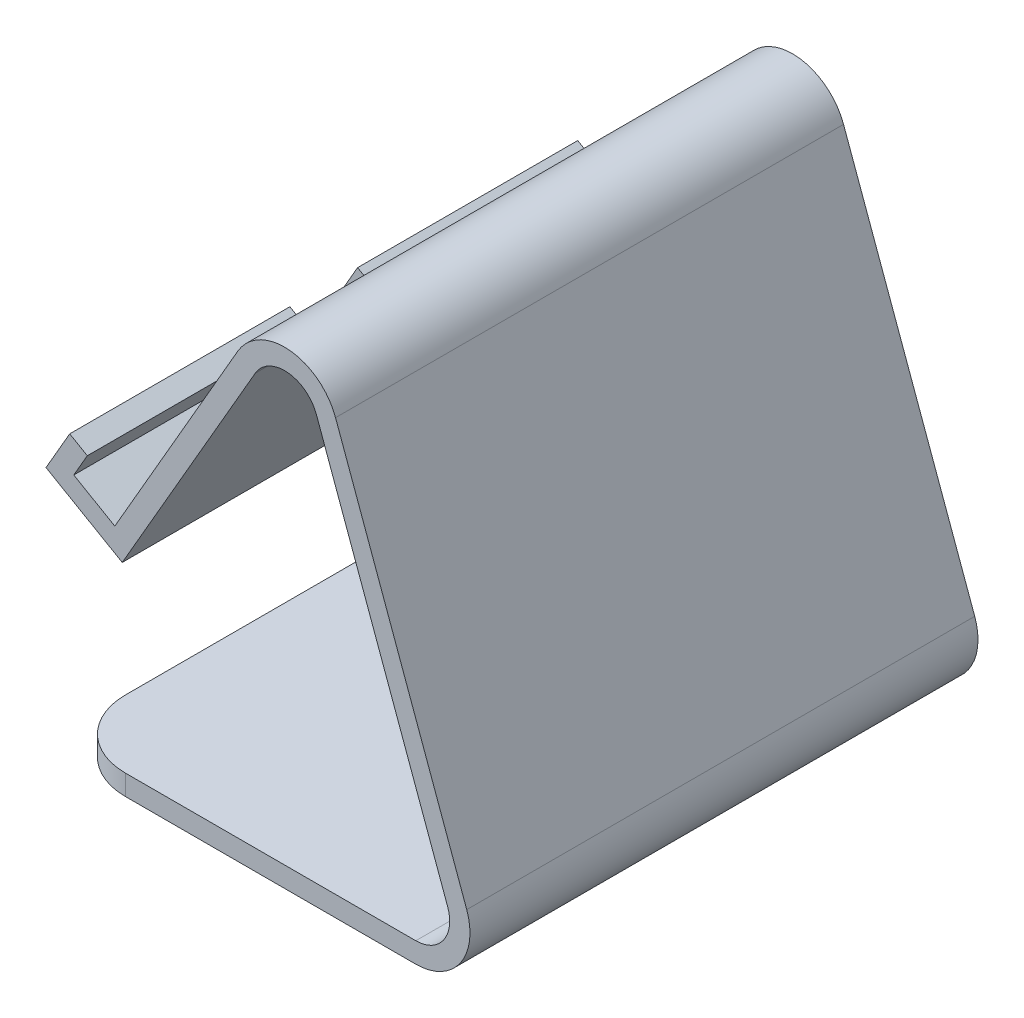
SolidWorks part; units mm, degrees
ref_plane "前视基准面" through (0, 0, 0) normal (0, 0, 1) x (1, 0, 0)
ref_plane "上视基准面" through (0, 0, 0) normal (0, 1, 0) x (1, 0, 0)
ref_plane "右视基准面" through (0, 0, 0) normal (1, 0, 0) x (0, 0, -1)
other "Configuration Table"
sketch "草图1" plane through (0, 0, 0) normal (0, 0, 1) x (1, 0, 0)
  line L0 (0, 0) -> (52.8593, 0)
  line L1 (57.5577, 6.7101) -> (38.1894, 59.9241)
  line L2 (29.1608, 60.714) -> (9.5221, 26.6987)
  line L3 (9.5221, 26.6987) -> (-1.7362, 33.1987)
  line L4 (-1.7362, 33.1987) -> (1.7638, 39.2609)
  line L5 (0, -3) -> (52.8593, -3)
  line L6 (60.3768, 7.7362) -> (41.0085, 60.9502)
  line L7 (26.5627, 62.214) -> (8.424, 30.7968)
  line L8 (8.424, 30.7968) -> (2.3618, 34.2968)
  line L9 (2.3618, 34.2968) -> (4.3618, 37.7609)
  line L10 (1.7638, 39.2609) -> (4.3618, 37.7609)
  line L11 (0, 0) -> (0, -3)
  arc A0 (38.1894, 59.9241) -> (29.1608, 60.714) centre (33.4909, 58.214) ccw
  arc A1 (52.8593, 0) -> (57.5577, 6.7101) centre (52.8593, 5) ccw
  arc A2 (52.8593, -3) -> (60.3768, 7.7362) centre (52.8593, 5) ccw
  arc A3 (41.0085, 60.9502) -> (26.5627, 62.214) centre (33.4909, 58.214) ccw
  point P9 (34.5221, 70)
  point P12 (60, 0)
  dimension "D8" = 5
  dimension "D9" = 5
  dimension "D1" = 60
  dimension "D2" = 70
  dimension "D3" = 70
  dimension "D4" = 50
  dimension "D5" = 13
  dimension "D6" = 7
  dimension "D7" = 50
  dimension "D10" = 3
extrude "凸台-拉伸2" add sketch "草图1" along normal mid plane 75
sketch "草图2" plane through (-15.6777, 9.0515, 0) normal (-0.866, 0.5, 0) x (0, 0, 1)
  line L0 (37.5, 27.8828) -> (-37.5, 27.8828) construction
  line L1 (-5, 35.3828) -> (5, 35.3828)
  line L2 (-5, 35.3828) -> (-5, 20.3828)
  line L3 (-5, 20.3828) -> (5, 20.3828)
  line L4 (5, 35.3828) -> (5, 20.3828)
  line L5 (-5, 35.3828) -> (5, 20.3828) construction
  line L6 (-5, 20.3828) -> (5, 35.3828) construction
  point P0 (0, 27.8828)
  point P9 (0, 0)
  dimension "D1" = 15
  dimension "D2" = 10
extrude "切除-拉伸2" cut sketch "草图2" against normal blind 20
fillet "圆角1" radius 10 1 edges at (0, -1.5, -37.5)
fillet "圆角2" radius 10 1 edges at (0, -1.5, 37.5)
sketch "草图3" plane through (-7.0174, 4.0515, 0) normal (-0.866, 0.5, 0) x (0, 0, 1)
  line L0 (-1.3419, 59.0526) -> (-10.7351, 45.2144)
  line L2 (6.1223, 45.2144) -> (-10.7351, 45.2144)
  line L3 (-1.3419, 59.0526) -> (6.1223, 45.2144)
extrude "切除-拉伸3" cut sketch "草图3" against normal blind 15
